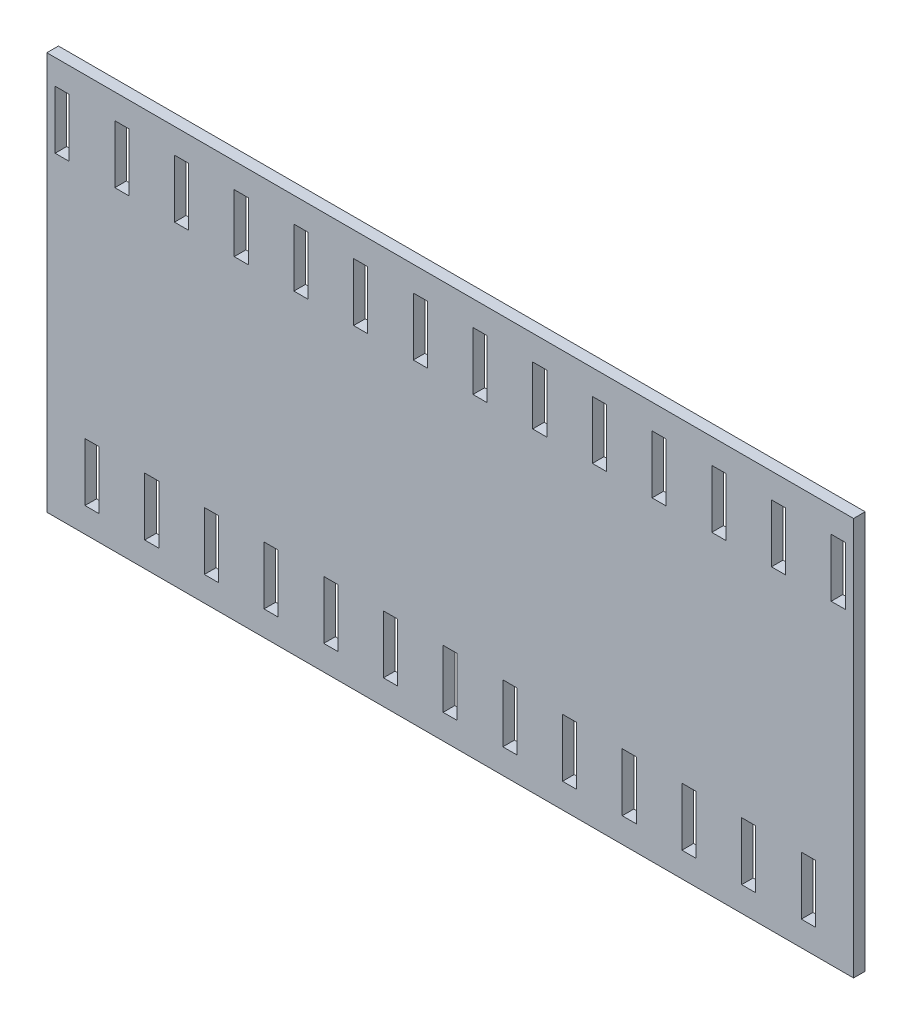
SolidWorks part; units mm, degrees
ref_plane "Plan de face" through (0, 0, 0) normal (0, 0, 1) x (1, 0, 0)
ref_plane "Plan de dessus" through (0, 0, 0) normal (0, 1, 0) x (1, 0, 0)
ref_plane "Plan de droite" through (0, 0, 0) normal (1, 0, 0) x (0, 0, -1)
sketch "Esquisse1" plane through (0, 0, 0) normal (0, 0, 1) x (1, 0, 0)
  line L1 (-48.65, -24) -> (48.65, -24)
  line L2 (-48.65, -24) -> (-48.65, 24)
  line L3 (-48.65, 24) -> (48.65, 24)
  line L4 (48.65, -24) -> (48.65, 24)
  line L5 (-48.65, -24) -> (48.65, 24) construction
  line L6 (-48.65, 24) -> (48.65, -24) construction
  point P0 (0, 0)
  dimension "D1" = 97.3
  dimension "D2" = 48
extrude "Boss.-Extru.1" add sketch "Esquisse1" along normal blind 1.4
sketch "Esquisse2" plane through (0, 0, 0) normal (0, 0, -1) x (-1, 0, 0)
  line L0 (-48.65, -24) -> (-48.65, 24) construction
  line L1 (-47.65, 21) -> (-45.95, 21)
  line L2 (-47.65, 21) -> (-47.65, 14)
  line L3 (-47.65, 14) -> (-45.95, 14)
  line L4 (-45.95, 21) -> (-45.95, 14)
  line L5 (-48.65, 24) -> (48.65, 24) construction
  line L6 (-40.45, 21) -> (-40.45, 14)
  line L7 (-40.45, 21) -> (-38.75, 21)
  line L8 (-38.75, 21) -> (-38.75, 14)
  line L9 (-40.45, 14) -> (-38.75, 14)
  line L10 (-33.25, 21) -> (-33.25, 14)
  line L11 (-33.25, 21) -> (-31.55, 21)
  line L12 (-31.55, 21) -> (-31.55, 14)
  line L13 (-33.25, 14) -> (-31.55, 14)
  line L14 (-26.05, 21) -> (-26.05, 14)
  line L15 (-26.05, 21) -> (-24.35, 21)
  line L16 (-24.35, 21) -> (-24.35, 14)
  line L17 (-26.05, 14) -> (-24.35, 14)
  line L18 (-18.85, 21) -> (-18.85, 14)
  line L19 (-18.85, 21) -> (-17.15, 21)
  line L20 (-17.15, 21) -> (-17.15, 14)
  line L21 (-18.85, 14) -> (-17.15, 14)
  line L22 (-11.65, 21) -> (-11.65, 14)
  line L23 (-11.65, 21) -> (-9.95, 21)
  line L24 (-9.95, 21) -> (-9.95, 14)
  line L25 (-11.65, 14) -> (-9.95, 14)
  line L26 (-4.45, 21) -> (-4.45, 14)
  line L27 (-4.45, 21) -> (-2.75, 21)
  line L28 (-2.75, 21) -> (-2.75, 14)
  line L29 (-4.45, 14) -> (-2.75, 14)
  line L30 (2.75, 21) -> (2.75, 14)
  line L31 (2.75, 21) -> (4.45, 21)
  line L32 (4.45, 21) -> (4.45, 14)
  line L33 (2.75, 14) -> (4.45, 14)
  line L34 (9.95, 21) -> (9.95, 14)
  line L35 (9.95, 21) -> (11.65, 21)
  line L36 (11.65, 21) -> (11.65, 14)
  line L37 (9.95, 14) -> (11.65, 14)
  line L38 (17.15, 21) -> (17.15, 14)
  line L39 (17.15, 21) -> (18.85, 21)
  line L40 (18.85, 21) -> (18.85, 14)
  line L41 (17.15, 14) -> (18.85, 14)
  line L42 (24.35, 21) -> (24.35, 14)
  line L43 (24.35, 21) -> (26.05, 21)
  line L44 (26.05, 21) -> (26.05, 14)
  line L45 (24.35, 14) -> (26.05, 14)
  line L46 (31.55, 21) -> (31.55, 14)
  line L47 (31.55, 21) -> (33.25, 21)
  line L48 (33.25, 21) -> (33.25, 14)
  line L49 (31.55, 14) -> (33.25, 14)
  line L50 (38.75, 21) -> (38.75, 14)
  line L51 (38.75, 21) -> (40.45, 21)
  line L52 (40.45, 21) -> (40.45, 14)
  line L53 (38.75, 14) -> (40.45, 14)
  line L54 (45.95, 21) -> (45.95, 14)
  line L55 (45.95, 21) -> (47.65, 21)
  line L56 (47.65, 21) -> (47.65, 14)
  line L57 (45.95, 14) -> (47.65, 14)
  line L58 (48.65, -24) -> (-48.65, -24) construction
  line L59 (-44.05, -14) -> (-42.35, -14)
  line L60 (-44.05, -14) -> (-44.05, -21)
  line L61 (-44.05, -21) -> (-42.35, -21)
  line L62 (-42.35, -14) -> (-42.35, -21)
  line L63 (-36.85, -14) -> (-36.85, -21)
  line L64 (-36.85, -14) -> (-35.15, -14)
  line L65 (-35.15, -14) -> (-35.15, -21)
  line L66 (-36.85, -21) -> (-35.15, -21)
  line L67 (-29.65, -14) -> (-29.65, -21)
  line L68 (-29.65, -14) -> (-27.95, -14)
  line L69 (-27.95, -14) -> (-27.95, -21)
  line L70 (-29.65, -21) -> (-27.95, -21)
  line L71 (-22.45, -14) -> (-22.45, -21)
  line L72 (-22.45, -14) -> (-20.75, -14)
  line L73 (-20.75, -14) -> (-20.75, -21)
  line L74 (-22.45, -21) -> (-20.75, -21)
  line L75 (-15.25, -14) -> (-15.25, -21)
  line L76 (-15.25, -14) -> (-13.55, -14)
  line L77 (-13.55, -14) -> (-13.55, -21)
  line L78 (-15.25, -21) -> (-13.55, -21)
  line L79 (-8.05, -14) -> (-8.05, -21)
  line L80 (-8.05, -14) -> (-6.35, -14)
  line L81 (-6.35, -14) -> (-6.35, -21)
  line L82 (-8.05, -21) -> (-6.35, -21)
  line L83 (-0.85, -14) -> (-0.85, -21)
  line L84 (-0.85, -14) -> (0.85, -14)
  line L85 (0.85, -14) -> (0.85, -21)
  line L86 (-0.85, -21) -> (0.85, -21)
  line L87 (6.35, -14) -> (6.35, -21)
  line L88 (6.35, -14) -> (8.05, -14)
  line L89 (8.05, -14) -> (8.05, -21)
  line L90 (6.35, -21) -> (8.05, -21)
  line L91 (13.55, -14) -> (13.55, -21)
  line L92 (13.55, -14) -> (15.25, -14)
  line L93 (15.25, -14) -> (15.25, -21)
  line L94 (13.55, -21) -> (15.25, -21)
  line L95 (20.75, -14) -> (20.75, -21)
  line L96 (20.75, -14) -> (22.45, -14)
  line L97 (22.45, -14) -> (22.45, -21)
  line L98 (20.75, -21) -> (22.45, -21)
  line L99 (27.95, -14) -> (27.95, -21)
  line L100 (27.95, -14) -> (29.65, -14)
  line L101 (29.65, -14) -> (29.65, -21)
  line L102 (27.95, -21) -> (29.65, -21)
  line L103 (35.15, -14) -> (35.15, -21)
  line L104 (35.15, -14) -> (36.85, -14)
  line L105 (36.85, -14) -> (36.85, -21)
  line L106 (35.15, -21) -> (36.85, -21)
  line L107 (42.35, -14) -> (42.35, -21)
  line L108 (42.35, -14) -> (44.05, -14)
  line L109 (44.05, -14) -> (44.05, -21)
  line L110 (42.35, -21) -> (44.05, -21)
  dimension "D1" = 1
  dimension "D2" = 7
  dimension "D3" = 1.7
  dimension "D4" = 3
  dimension "D6" = 4.6
  dimension "D7" = 3
  dimension "D8" = 7
  dimension "D9" = 1.7
  dimension "D5" = 14
  dimension "D10" = 13
extrude "Enlèv. mat.-Extru.1" cut sketch "Esquisse2" against normal through all
sketch "Esquisse3" plane through (0, 0, 0) normal (0, 0, -1) x (-1, 0, 0)
  text T0 "KR   DRIFT"
extrude "Enlèv. mat.-Extru.2" cut sketch "Esquisse3" against normal blind 0.1
